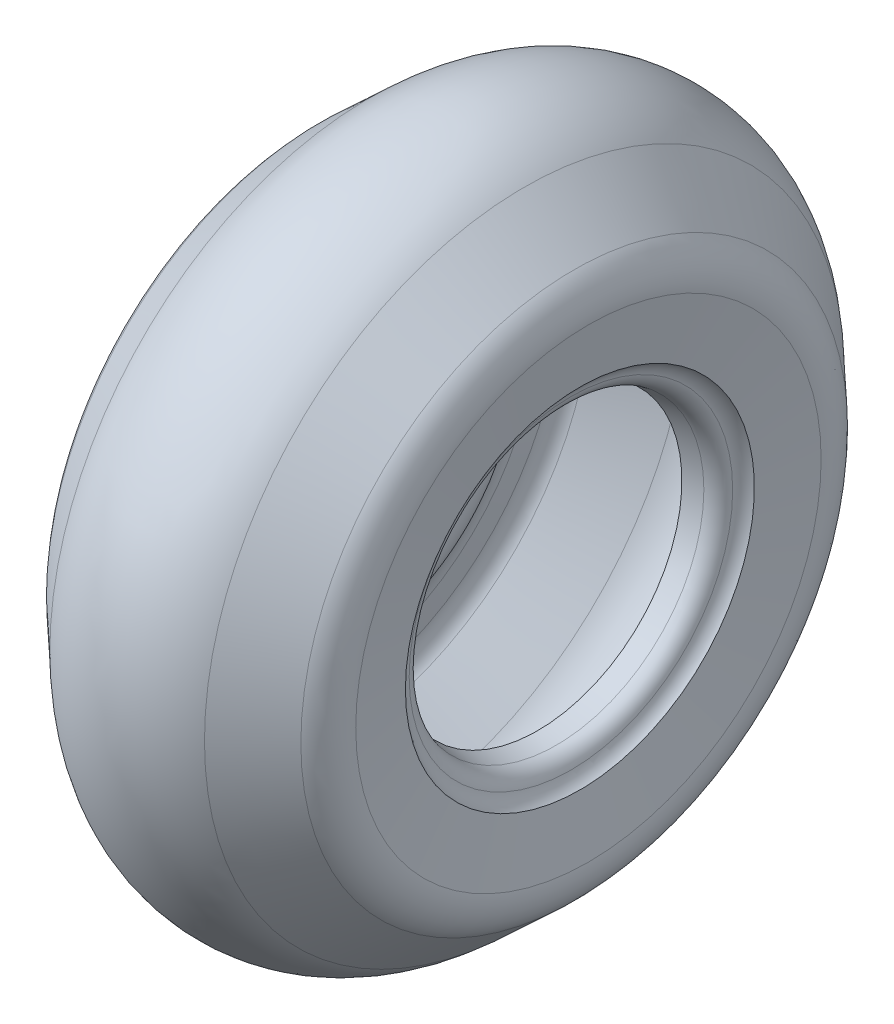
SolidWorks part; units mm, degrees
material "Silicon Rubber"
ref_plane "Front Plane" through (0, 0, 0) normal (0, 0, 1) x (1, 0, 0)
ref_plane "Top Plane" through (0, 0, 0) normal (0, 1, 0) x (1, 0, 0)
ref_plane "Right Plane" through (0, 0, 0) normal (1, 0, 0) x (0, 0, -1)
sketch "Sketch3" plane through (0, 0, 0) normal (0, 1, 0) x (1, 0, 0)
  line L0 (0, 0) -> (112.5523, 0) construction
  line L5 (-64.3595, -266.2421) -> (-105.8736, -227.5296)
  line L6 (-117.7348, -193.7001) -> (-110.6175, -145.2513)
  line L23 (-58.5114, -259.9708) -> (-100.0255, -221.2582)
  line L28 (0, 0) -> (0, -291.594) construction
  line L32 (106.6301, -201.376) -> (102.5217, -178.6522)
  line L33 (90.895, -122.9238) -> (75.46, -120.094)
  line L34 (58.5114, -259.9708) -> (100.0255, -221.2582)
  line L35 (117.7348, -193.7001) -> (110.6175, -145.2513)
  line L36 (64.3595, -266.2421) -> (105.8736, -227.5296)
  line L38 (-90.895, -122.9238) -> (-75.46, -120.094)
  line L41 (-106.6301, -201.376) -> (-102.5217, -178.6522)
  arc A4 (-64.3595, -266.2421) -> (64.3595, -266.2421) centre (0, -197.225) ccw
  arc A7 (-105.8736, -227.5296) -> (-117.7348, -193.7001) centre (-79.557, -199.3085) cw
  arc A13 (-100.0255, -221.2582) -> (-106.6301, -201.376) centre (-85.1127, -205.2663) cw
  arc A17 (-58.5114, -259.9708) -> (58.5114, -259.9708) centre (0, -197.225) ccw
  arc A18 (87.8423, -148.9247) -> (75.46, -120.094) centre (123.3527, -116.5992) cw
  arc A19 (102.5217, -178.6522) -> (87.8423, -148.9247) centre (43.4544, -189.3315) ccw
  arc A20 (90.895, -122.9238) -> (103.1549, -134.6504) centre (88.1116, -138.1057) cw
  arc A21 (-110.6175, -145.2513) -> (-103.1549, -134.6504) centre (-119.8696, -130.8111) ccw
  arc A22 (-90.895, -122.9238) -> (-103.1549, -134.6504) centre (-88.1116, -138.1057) ccw
  arc A23 (110.6175, -145.2513) -> (103.1549, -134.6504) centre (119.8696, -130.8111) cw
  arc A24 (100.0255, -221.2582) -> (106.6301, -201.376) centre (85.1127, -205.2663) ccw
  arc A25 (105.8736, -227.5296) -> (117.7348, -193.7001) centre (79.557, -199.3085) ccw
  arc A26 (-102.5217, -178.6522) -> (-87.8423, -148.9247) centre (-43.4544, -189.3315) cw
  arc A27 (-87.8423, -148.9247) -> (-75.46, -120.094) centre (-123.3527, -116.5992) ccw
  point P3 (0, -291.594)
  dimension "D3" = 38.5875
  dimension "D5" = 21.8663
  dimension "D8" = 60.025
  dimension "D9" = 48.02
  dimension "D11" = 17.15
  dimension "D12" = 15.435
  dimension "D4" = 394.45
  dimension "SECTON HEIGHT" = 171.5
  dimension "D6" = 22.7237
  dimension "D7" = 48.4487
  dimension "D10" = 15.6922
  dimension "D13" = 47
  dimension "D14" = 75.46
  dimension "D15" = 11.1046
  dimension "D16" = 22.7752
  dimension "D17" = 90.895
  dimension "D18" = 110.6175
  dimension "D19" = 117.7348
  dimension "D1" = 8.575
revolve "Revolve2" add sketch "Sketch3" angle 360 about L0
equation "\"D5@Sketch3\"=\"SECTON HEIGHT@Sketch3\"*255/2000"
equation "\"D1@Sketch3\"=\"SECTON HEIGHT@Sketch3\"*1/20"
equation "\"D3@Sketch3\"=\"SECTON HEIGHT@Sketch3\"*45/200"
equation "\"D15@Sketch3\"=\"SECTON HEIGHT@Sketch3\"*1295/20000"
equation "\"D7@Sketch3\"=\"SECTON HEIGHT@Sketch3\"*565/2000"
equation "\"D6@Sketch3\"=\"SECTON HEIGHT@Sketch3\"*265/2000"
equation "\"D8@Sketch3\"=\"SECTON HEIGHT@Sketch3\"*7/20"
equation "\"D9@Sketch3\"=\"SECTON HEIGHT@Sketch3\"*56/200"
equation "\"D18@Sketch3\"=\"SECTON HEIGHT@Sketch3\"*129/200"
equation "\"D16@Sketch3\"=\"SECTON HEIGHT@Sketch3\"*2656/20000"
equation "\"D11@Sketch3\"=\"SECTON HEIGHT@Sketch3\"*1/10"
equation "\"D14@Sketch3\"=\"SECTON HEIGHT@Sketch3\"*88/200"
equation "\"D17@Sketch3\"=\"SECTON HEIGHT@Sketch3\"*106/200"
equation "\"D10@Sketch3\"=\"SECTON HEIGHT@Sketch3\"*183/2000"
equation "\"D12@Sketch3\"=\"SECTON HEIGHT@Sketch3\"*18/200"
equation "\"D19@Sketch3\"=\"SECTON HEIGHT@Sketch3\"*1373/2000"
equation "\"D4@Sketch3\"=\"SECTON HEIGHT@Sketch3\"*46/20"
